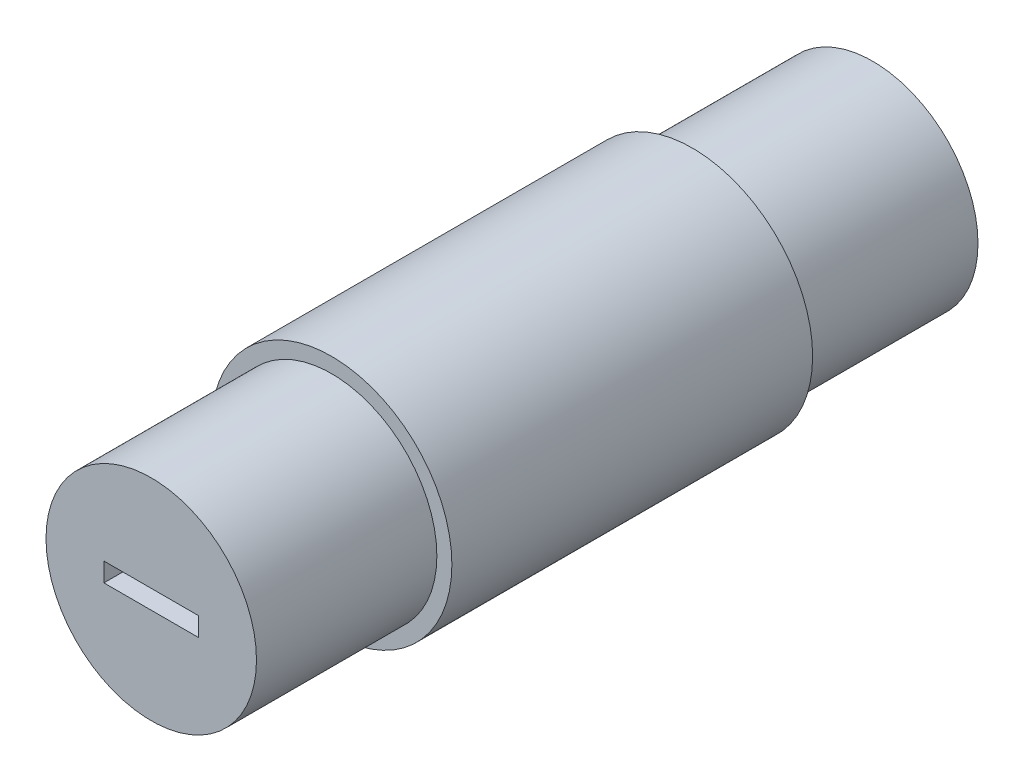
SolidWorks part; units mm, degrees
ref_plane "Front" through (0, 0, 0) normal (0, 0, 1) x (1, 0, 0)
ref_plane "Top" through (0, 0, 0) normal (0, 1, 0) x (1, 0, 0)
ref_plane "Right" through (0, 0, 0) normal (1, 0, 0) x (0, 0, -1)
sketch "Sketch1" plane through (0, 0, 0) normal (0, 0, 1) x (1, 0, 0)
  circle A0 centre (0, 0) radius 12.7
  dimension "D1" = 25.4
extrude "Base-Extrude" add sketch "Sketch1" along normal mid plane 76.2
sketch "Sketch2" plane through (0, 0, 38.1) normal (0, 0, 1) x (1, 0, 0)
  circle A0 centre (0, 0) radius 11.115
  circle A1 centre (0, 0) radius 12.7
  circle A2 centre (0, 0) radius 12.7 construction
  dimension "D1" = 1.585
extrude "Cut-Extrude1" cut sketch "Sketch2" against normal blind 19.05
mirror "Mirror1" about plane through (0, 0, 0) normal (0, 0, 1) of "Cut-Extrude1"
sketch "Sketch3" plane through (0, 0, 38.1) normal (0, 0, 1) x (1, 0, 0)
  line L0 (0, 2.1312) -> (0, -2.444) construction
  line L1 (-5, 1) -> (5, 1)
  line L2 (-5, 1) -> (-5, -1)
  line L3 (-5, -1) -> (5, -1)
  line L4 (5, 1) -> (5, -1)
  line L5 (-1.8379, 0) -> (2.268, 0) construction
  dimension "D1" = 2
  dimension "D2" = 10
extrude "Slot for Flat Blade Screw Driver" cut sketch "Sketch3" against normal blind 6
mirror "Mirror2" about plane through (0, 0, 0) normal (0, 0, 1) of "Slot for Flat Blade Screw Driver"
